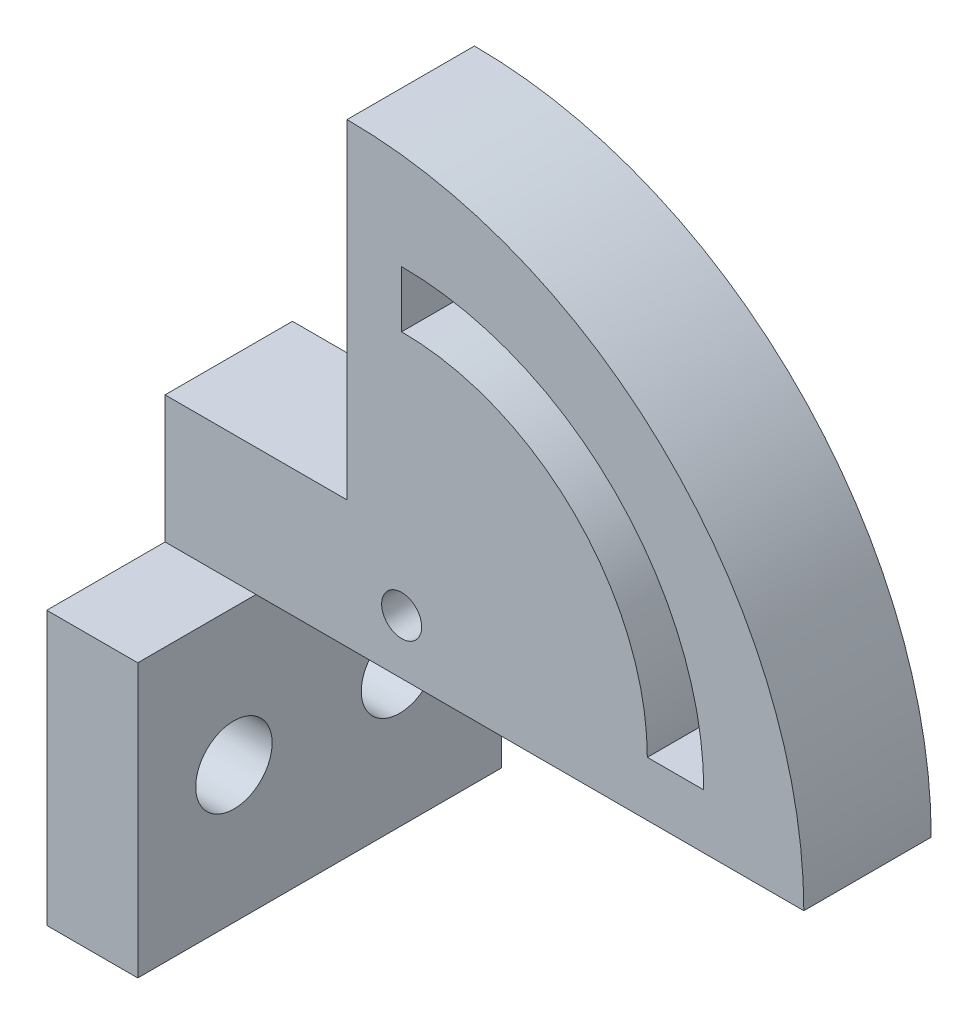
SolidWorks part; units mm, degrees
ref_plane "Front Plane" through (0, 0, 0) normal (0, 0, 1) x (1, 0, 0)
ref_plane "Top Plane" through (0, 0, 0) normal (0, 1, 0) x (1, 0, 0)
ref_plane "Right Plane" through (0, 0, 0) normal (1, 0, 0) x (0, 0, -1)
sketch "Sketch1" plane through (0, 0, 0) normal (0, 1, 0) x (1, 0, 0)
  line L1 (0, 0) -> (25.1, 0)
  line L2 (0, 0) -> (0, 7)
  line L3 (0, 7) -> (25.1, 7)
  line L4 (25.1, 0) -> (25.1, 7)
revolve "Revolve1" add sketch "Sketch1" angle 90 about L2
sketch "Sketch2" plane through (0, 0, 0) normal (-1, 0, 0) x (0, 0, 1)
  line L0 (-7, 25.1) -> (-7, 0) construction
  line L1 (0, 0) -> (-7, 0)
  line L2 (0, 0) -> (0, 7)
  line L3 (0, 7) -> (-7, 7)
  line L4 (-7, 0) -> (-7, 7)
extrude "Boss-Extrude1" add sketch "Sketch2" along normal blind 10
sketch "Sketch6" plane through (0, 0, 0) normal (0, -1, 0) x (-1, 0, 0)
  line L5 (-25.1, 7) -> (10, 7) construction
  line L6 (10, 0) -> (5, 0)
  line L7 (10, 0) -> (10, 7)
  line L8 (10, 7) -> (5, 7)
  line L9 (5, 0) -> (5, 7)
extrude "Boss-Extrude2" add sketch "Sketch6" along normal blind 15
sketch "Sketch7" plane through (0, 0, 0) normal (0, 0, 1) x (1, 0, 0)
  line L1 (-5, 0) -> (-10, 0)
  line L2 (-5, 0) -> (-5, -15)
  line L3 (-5, -15) -> (-10, -15)
  line L4 (-10, 0) -> (-10, -15)
extrude "Boss-Extrude3" add sketch "Sketch7" along normal blind 6.5
sketch "Sketch8" plane through (0, 0, -7) normal (0, 0, -1) x (-1, 0, 0)
  line L1 (5, 0) -> (10, 0)
  line L2 (5, 0) -> (5, -15)
  line L3 (5, -15) -> (10, -15)
  line L4 (10, 0) -> (10, -15)
extrude "Boss-Extrude4" add sketch "Sketch8" along normal blind 6.5
sketch "Sketch10" plane through (-5, 0, 0) normal (1, 0, 0) x (0, 0, -1)
  circle A1 centre (-1.216, -7.5) radius 2.1
  circle A2 centre (7.882, -7.5) radius 2.1
extrude "Cut-Extrude8" cut sketch "Sketch10" against normal blind 18.5
sketch "Sketch12" plane through (0, 0, 0) normal (0, 0, 1) x (1, 0, 0)
  line L0 (3, 16.5) -> (3, 19.6)
  line L1 (16.5, 3) -> (19.6, 3)
  circle A0 centre (3, 3) radius 1.1
  arc A1 (16.5, 3) -> (3, 16.5) centre (3, 3) ccw
  arc A2 (19.6, 3) -> (3, 19.6) centre (3, 3) ccw
extrude "Cut-Extrude11" cut sketch "Sketch12" against normal blind 10
